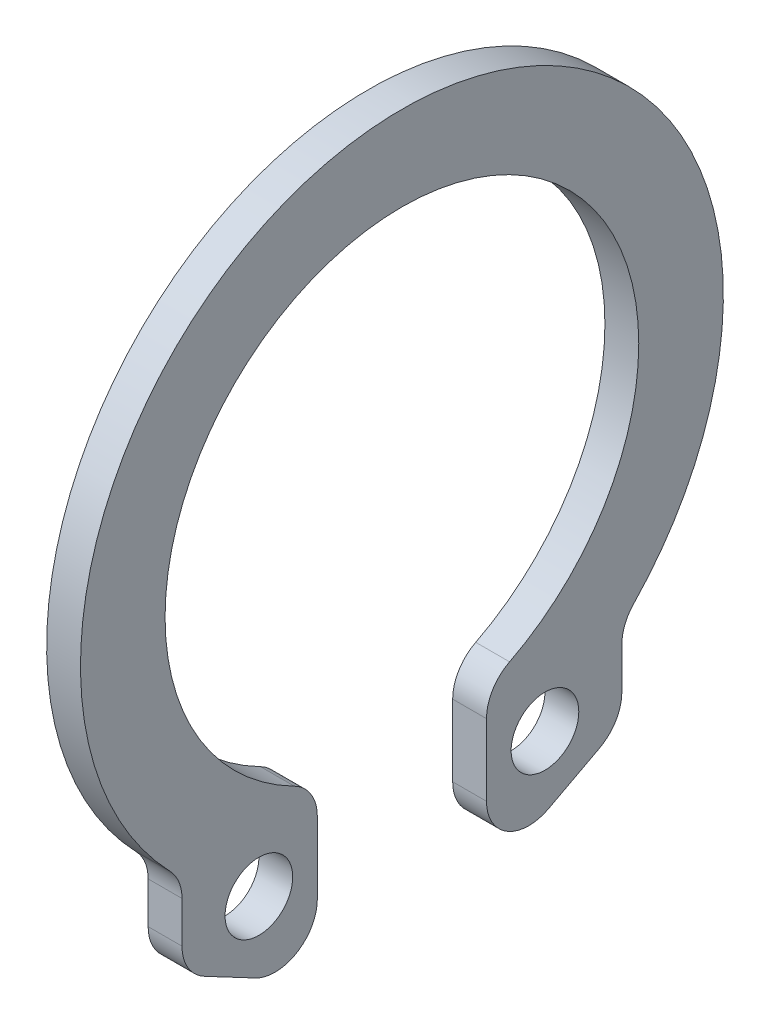
SolidWorks part; units mm, degrees
material "Alloy Steel"
ref_plane "Front" through (0, 0, 0) normal (0, 0, 1) x (1, 0, 0)
ref_plane "Top" through (0, 0, 0) normal (0, 1, 0) x (1, 0, 0)
ref_plane "Right" through (0, 0, 0) normal (1, 0, 0) x (0, 0, -1)
sketch "Sketch1" plane through (0, 0, 0) normal (1, 0, 0) x (0, 0, -1)
  line L0 (1.3, -1.3856) -> (1.3, -1.885)
  line L1 (1.3, -1.885) -> (0.5, -2.3077)
  line L2 (0.5, -2.3077) -> (0.5, -1.3077)
  line L3 (0, 0.6241) -> (0, -2.7452) construction
  line L4 (-0.5, -2.3077) -> (-0.5, -1.3077)
  line L5 (-1.3, -1.885) -> (-0.5, -2.3077)
  line L6 (-1.3, -1.3856) -> (-1.3, -1.885)
  line L7 (0.5, -1.7064) -> (1.3, -1.7064) construction
  arc A0 (-0.5, -1.3077) -> (0.5, -1.3077) centre (0, 0) cw
  arc A1 (-1.3, -1.3856) -> (1.3, -1.3856) centre (0, 0) cw
  circle A2 centre (0.8455, -1.7064) radius 0.2
  circle A3 centre (-0.8455, -1.7064) radius 0.2
  dimension "D1" = 1.4
  dimension "D2" = 0.5
  dimension "D7" = 0.4
  dimension "D3" = 0.4994
  dimension "D4" = 1
  dimension "D5" = 1
  dimension "D6" = 0.8
extrude "Boss-Extrude1" add sketch "Sketch1" along normal blind 0.2
fillet "Fillet1" radius 0.25 8 edges at (0.1, -1.3856, -1.3) (0.1, -1.885, -1.3) (0.1, -2.3077, -0.5) (0.1, -1.3077, -0.5) (0.1, -1.3856, 1.3) (0.1, -1.885, 1.3) (0.1, -2.3077, 0.5) (0.1, -1.3077, 0.5)
